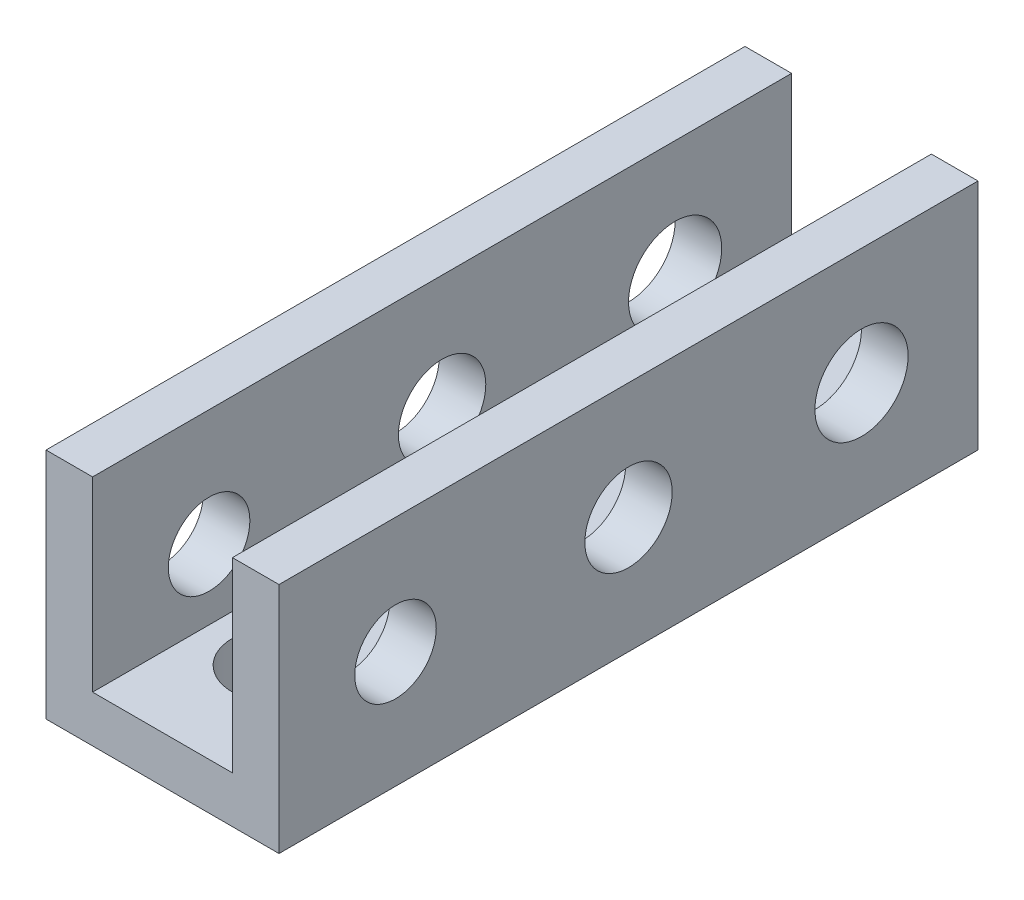
SolidWorks part; units mm, degrees
ref_plane "Front Plane" through (0, 0, 0) normal (0, 0, 1) x (1, 0, 0)
ref_plane "Top Plane" through (0, 0, 0) normal (0, 1, 0) x (1, 0, 0)
ref_plane "Right Plane" through (0, 0, 0) normal (1, 0, 0) x (0, 0, -1)
sketch "Sketch1" plane through (0, 0, 0) normal (0, 0, 1) x (1, 0, 0)
  line L0 (3, 1) -> (-3, 1)
  line L1 (-3, 1) -> (-3, 9)
  line L2 (-3, 9) -> (-5, 9)
  line L3 (-5, 9) -> (-5, -1)
  line L4 (-5, -1) -> (5, -1)
  line L5 (0, 1) -> (0, -1) construction
  line L6 (5, 9) -> (5, -1)
  line L7 (3, 9) -> (5, 9)
  line L8 (3, 1) -> (3, 9)
  point P6 (0, 0)
  dimension "D1" = 2
  dimension "D2" = 10
  dimension "D3" = 2
  dimension "D4" = 10
extrude "Boss-Extrude1" add sketch "Sketch1" along normal blind 30
sketch "Sketch2" plane through (-3, 0, 0) normal (1, 0, 0) x (0, 0, -1)
  line L0 (-30, 9) -> (0, 9) construction
  line L1 (-30, -1) -> (-30, 9) construction
  line L2 (0, -1) -> (0, 9) construction
  circle A0 centre (-25, 4) radius 1.75
  circle A1 centre (-5, 4) radius 2
  circle A2 centre (-15, 4) radius 1.875
  dimension "D3" = 3.5
  dimension "D4" = 4
  dimension "D8" = 3.75
  dimension "D1" = 5
  dimension "D2" = 5
  dimension "D5" = 5
  dimension "D6" = 5
  dimension "D7" = 10
extrude "Cut-Extrude2" cut sketch "Sketch2" against normal through all both and the other way through all
sketch "Sketch3" plane through (0, 1, 0) normal (0, 1, 0) x (1, 0, 0)
  line L0 (3, 0) -> (-3, 0) construction
  line L1 (3, -30) -> (-3, -30) construction
  circle A0 centre (0, -5) radius 1.75
  circle A1 centre (0, -15) radius 1.875
  circle A2 centre (0, -25) radius 2
  point P6 (0, 0)
  point P9 (0, 0)
  dimension "D1" = 3.5
  dimension "D2" = 3.75
  dimension "D3" = 4
  dimension "D4" = 5
  dimension "D5" = 10
  dimension "D6" = 5
extrude "Cut-Extrude3" cut sketch "Sketch3" against normal blind 10
